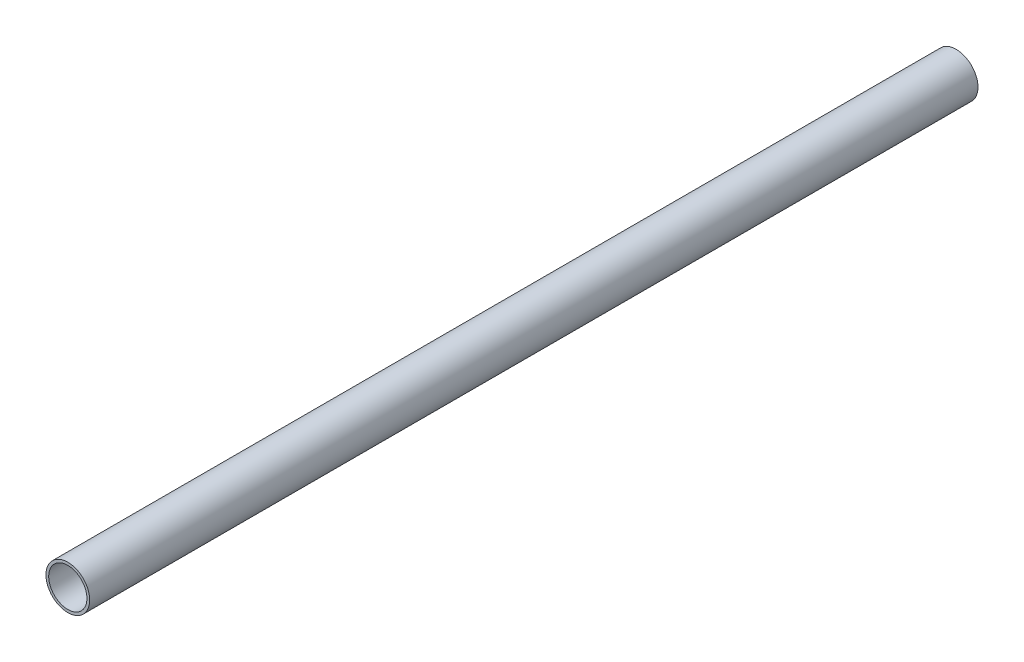
SolidWorks part; units mm, degrees
material "Thornel Mat VMA"
ref_plane "Front Plane" through (0, 0, 0) normal (0, 0, 1) x (1, 0, 0)
ref_plane "Top Plane" through (0, 0, 0) normal (0, 1, 0) x (1, 0, 0)
ref_plane "Right Plane" through (0, 0, 0) normal (1, 0, 0) x (0, 0, -1)
sketch "Sketch1" plane through (0, 0, 0) normal (0, 0, 1) x (1, 0, 0)
  circle A0 centre (0, 0) radius 8
  circle A1 centre (0, 0) radius 7
  dimension "D1" = 16
  dimension "D2" = 1
extrude "Boss-Extrude1" add sketch "Sketch1" along normal blind 325.28
